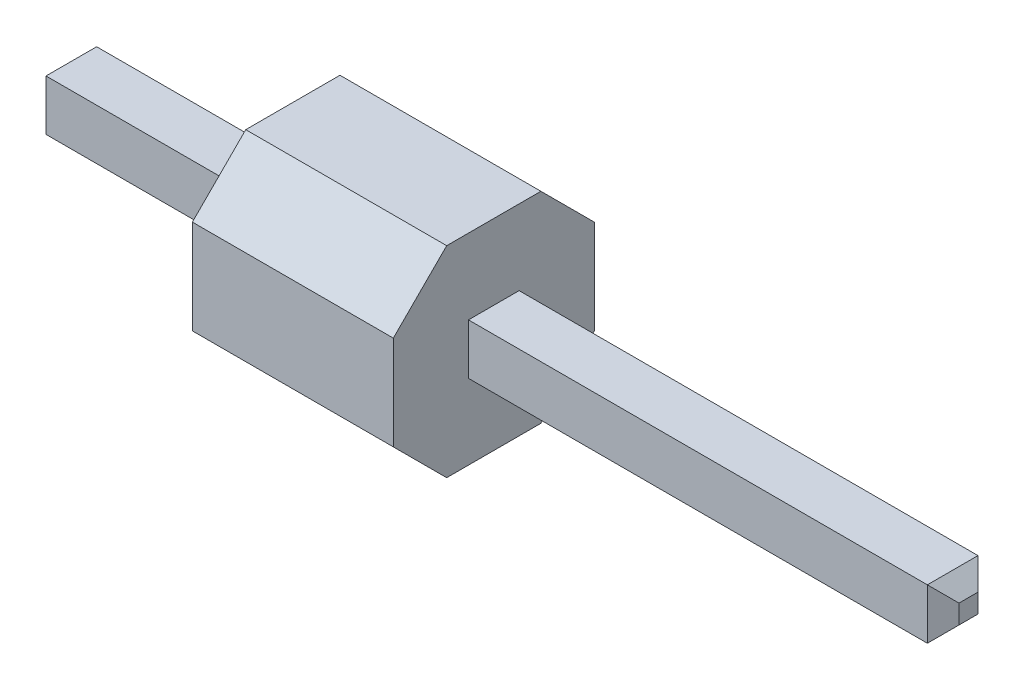
SolidWorks part; units mm, degrees
ref_plane "Alzado" through (0, 0, 0) normal (0, 0, 1) x (1, 0, 0)
ref_plane "Planta" through (0, 0, 0) normal (0, 1, 0) x (1, 0, 0)
ref_plane "Vista lateral" through (0, 0, 0) normal (1, 0, 0) x (0, 0, -1)
sketch "Croquis1" plane through (0, 0, 0) normal (1, 0, 0) x (0, 0, -1)
  line L0 (-0.5955, 1.27) -> (-1.27, 0.5955)
  line L1 (0.5955, 1.27) -> (-0.5955, 1.27)
  line L2 (1.27, 0.5955) -> (1.27, -0.5955)
  line L3 (0.5955, -1.27) -> (-0.5955, -1.27)
  line L4 (-1.27, 0.5955) -> (-1.27, -0.5955)
  line L5 (1.27, 1.27) -> (-1.27, -1.27) construction
  line L6 (1.27, -1.27) -> (-1.27, 1.27) construction
  line L7 (-0.5955, -1.27) -> (-1.27, -0.5955)
  line L8 (1.27, -0.5955) -> (0.5955, -1.27)
  line L9 (1.27, 0.5955) -> (0.5955, 1.27)
  line L12 (0, 0) -> (0, 2.4434) construction
  line L13 (1.27, 0.5955) -> (1.27, 2.4434) construction
  line L22 (0.32, 0.32) -> (-0.32, 0.32)
  line L23 (0.32, 0.32) -> (0.32, -0.32)
  line L24 (0.32, -0.32) -> (-0.32, -0.32)
  line L25 (-0.32, 0.32) -> (-0.32, -0.32)
  line L26 (0.32, 0.32) -> (-0.32, -0.32) construction
  line L27 (0.32, -0.32) -> (-0.32, 0.32) construction
  point P0 (0, 0)
  dimension "D1" = 2.54
  dimension "D2" = 2.54
  dimension "D4" = 0.64
  dimension "D5" = 0.64
extrude "Saliente-Extruir1" add sketch "Croquis1" along normal blind 2.54
sketch "Croquis2" plane through (0, 0, 0) normal (0, 1, 0) x (1, 0, 0)
  line L0 (0, 1.27) -> (0.5165, 1.27) construction
  line L1 (2.54, 1.27) -> (0, 1.27) construction
  line L2 (0.5165, 1.2433) -> (0.5165, 1.2967)
  line L3 (0.4575, 1.3879) -> (0, 1.5936)
  line L4 (0, 1.27) -> (0, 1.9445) construction
  line L5 (0.4575, 1.1521) -> (0, 0.9464)
  line L6 (0, 1.5936) -> (0, 0.9464)
  arc A0 (0.5165, 1.2967) -> (0.4575, 1.3879) centre (0.4165, 1.2967) ccw
  arc A1 (0.5165, 1.2433) -> (0.4575, 1.1521) centre (0.4165, 1.2433) cw
  dimension "D1" = 0.1
extrude "Cortar-Extruir1" cut sketch "Croquis2" against normal blind 2.54 and the other way blind 2.54
sketch "Croquis3" plane through (0, 0, 0) normal (1, 0, 0) x (0, 0, -1)
  line L1 (-0.32, -0.32) -> (0.32, -0.32)
  line L2 (-0.32, -0.32) -> (-0.32, 0.32)
  line L3 (-0.32, 0.32) -> (0.32, 0.32)
  line L4 (0.32, -0.32) -> (0.32, 0.32)
extrude "Saliente-Extruir2" add sketch "Croquis3" along normal blind 8.54 and the other way blind 3 separate body
chamfer "Chaflán1" distance 0.2 angle 45 8 edges at (-3, -0.32, 0) (-3, 0, -0.32) (-3, 0.32, 0) (-3, 0, 0.32) (8.54, 0.32, 0) (8.54, 0, -0.32) (8.54, -0.32, 0) (8.54, 0, 0.32)
